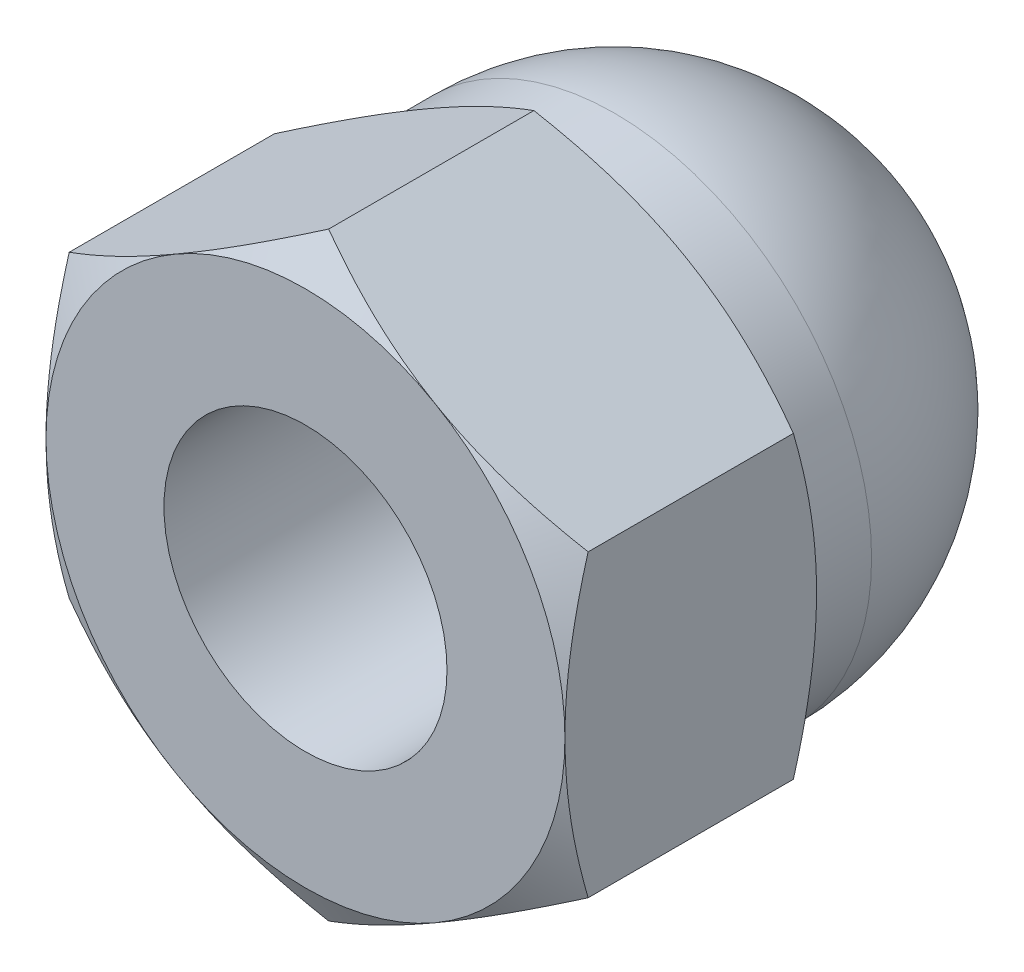
SolidWorks part; units mm, degrees
ref_plane "Front Plane" through (0, 0, 0) normal (0, 0, 1) x (1, 0, 0)
ref_plane "Top Plane" through (0, 0, 0) normal (0, 1, 0) x (1, 0, 0)
ref_plane "Right Plane" through (0, 0, 0) normal (1, 0, 0) x (0, 0, -1)
sketch "Sketch1" plane through (0, 0, 0) normal (0, 0, 1) x (1, 0, 0)
  line L1 (0, 3.1754) -> (-2.75, 1.5877)
  line L2 (-2.75, 1.5877) -> (-2.75, -1.5877)
  line L3 (-2.75, -1.5877) -> (0, -3.1754)
  line L4 (0, -3.1754) -> (2.75, -1.5877)
  line L5 (2.75, -1.5877) -> (2.75, 1.5877)
  line L6 (2.75, 1.5877) -> (0, 3.1754)
  circle A0 centre (0, 0) radius 2.75 construction
extrude "Extrude1" add sketch "Sketch1" against normal blind 2.6667
sketch "Sketch2" plane through (0, 0, 0) normal (0, 0, 1) x (1, 0, 0)
  circle A0 centre (0, 0) radius 2.75 construction
  circle A1 centre (0, 0) radius 2.75
extrude "Cut-Extrude1" cut sketch "Sketch2" against normal through all draft 60 flip side to cut
sketch "Sketch3" plane through (0, 0, -2.6667) normal (0, 0, -1) x (-1, 0, 0)
  circle A1 centre (0, 0) radius 2.75
  circle A2 centre (0, 0) radius 2.75
  dimension "D1" = 0
extrude "Cut-Extrude2" cut sketch "Sketch3" against normal through all draft 60 flip side to cut
sketch "Sketch14" plane through (0, 0, 0) normal (1, 0, 0) x (0, 0, -1)
  line L0 (2.6667, 2.7225) -> (2.6667, 0)
  line L1 (2.6667, 0) -> (6, 0)
  line L2 (2.6667, 0) -> (2.6667, 2.3816) construction
  line L3 (2.6667, 2.7225) -> (3.2775, 2.7225)
  line L6 (0, 0) -> (2.6667, 0) construction
  arc A0 (3.2775, 2.7225) -> (6, 0) centre (3.2775, 0) cw
  dimension "overall length" = 6
  dimension "D1" = 5.445
revolve "Revolve1" add sketch "Sketch14" angle 360 about L6
sketch "Sketch4" plane through (0, 0, 0) normal (0, 0, 1) x (1, 0, 0)
  circle A0 centre (0, 0) radius 1.5
  dimension "Thread Dia" = 3
extrude "Cut-Extrude3" cut sketch "Sketch4" against normal blind 3.8
equation "\"Nut Height@Extrude1\" = \"overall length@Sketch14\"/2.25"
equation "\"D1@Sketch14\" = \"Hex@Sketch1\"*.99"
